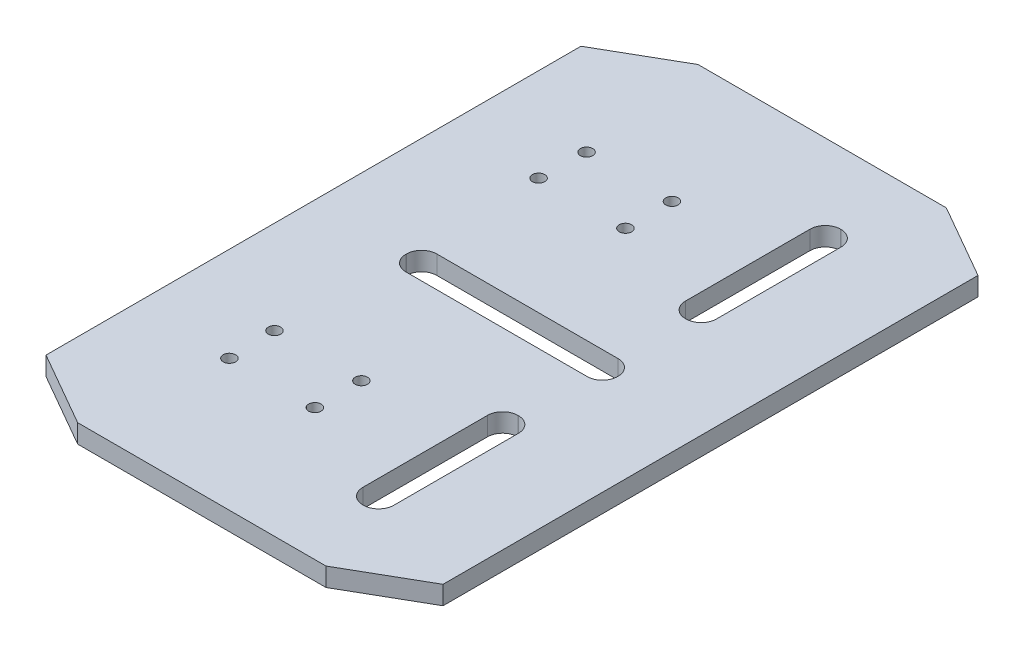
SolidWorks part; units mm, degrees
material "Custom Plastic"
ref_plane "Front Plane" through (0, 0, 0) normal (0, 0, 1) x (1, 0, 0)
ref_plane "Top Plane" through (0, 0, 0) normal (0, 1, 0) x (1, 0, 0)
ref_plane "Right Plane" through (0, 0, 0) normal (1, 0, 0) x (0, 0, -1)
sketch "Sketch1" plane through (0, 0, 0) normal (0, 1, 0) x (1, 0, 0)
  line L0 (-32, -43.1177) -> (-20.0119, -50)
  line L1 (-20.0119, -50) -> (20.0119, -50)
  line L2 (-32, -43.1177) -> (-32, 43.1177)
  line L3 (-20.0119, 50) -> (20.0119, 50)
  line L4 (32, -43.1177) -> (32, 43.1177)
  line L5 (-28.8545, -44.9235) -> (28.8545, 44.9235) construction
  line L6 (-28.4421, 45.1603) -> (28.4421, -45.1603) construction
  line L7 (-114.8204, 0) -> (150.9847, 0) construction
  line L8 (0, -72.5189) -> (0, 84.1411) construction
  line L9 (32, -43.1177) -> (20.0119, -50)
  line L10 (32, 43.1177) -> (20.0119, 50)
  line L11 (-32, 43.1177) -> (-20.0119, 50)
  point P0 (0, 0)
  dimension "D1" = 64
  dimension "D2" = 100
extrude "Boss-Extrude1" add sketch "Sketch1" along normal blind 3
sketch "Sketch5" plane through (0, 3, 0) normal (0, 1, 0) x (1, 0, 0)
  line L0 (-100.8141, 0) -> (111.641, 0) construction
  line L1 (14.5, 50) -> (14.5, -50) construction
  line L2 (-14.6202, -2.5) -> (14.6202, -2.5)
  line L3 (-17.0702, -0.05) -> (-17.0702, 0.05)
  line L4 (-14.6202, 2.5) -> (14.6202, 2.5)
  line L5 (17.0702, -0.05) -> (17.0702, 0.05)
  line L6 (-17.0702, -2.5) -> (17.0702, 2.5) construction
  line L7 (-17.0702, 2.5) -> (17.0702, -2.5) construction
  line L8 (20.0119, 50) -> (-20.0119, 50) construction
  line L9 (-20.0119, -50) -> (20.0119, -50) construction
  line L10 (14.5, 50) -> (14.5, 0) construction
  line L11 (14.5, 0) -> (14.5, -50) construction
  line L12 (14.45, -38.5) -> (14.55, -38.5)
  line L13 (14.45, 13.5) -> (14.55, 13.5)
  line L14 (12, 15.95) -> (12, 36.05)
  line L15 (14.45, 38.5) -> (14.55, 38.5)
  line L16 (17, 15.95) -> (17, 36.05)
  line L17 (12, 13.5) -> (17, 38.5) construction
  line L18 (12, 38.5) -> (17, 13.5) construction
  line L19 (12, -15.95) -> (12, -36.05)
  line L20 (14.45, -13.5) -> (14.55, -13.5)
  line L21 (17, -15.95) -> (17, -36.05)
  line L22 (32, -43.1177) -> (32, 43.1177) construction
  arc A0 (14.45, -38.5) -> (12, -36.05) centre (14.45, -36.05) cw
  arc A1 (14.55, -38.5) -> (17, -36.05) centre (14.55, -36.05) ccw
  arc A2 (12, -15.95) -> (14.45, -13.5) centre (14.45, -15.95) cw
  arc A3 (14.55, -13.5) -> (17, -15.95) centre (14.55, -15.95) cw
  arc A4 (-14.6202, -2.5) -> (-17.0702, -0.05) centre (-14.6202, -0.05) cw
  arc A5 (-17.0702, 0.05) -> (-14.6202, 2.5) centre (-14.6202, 0.05) cw
  arc A6 (14.6202, 2.5) -> (17.0702, 0.05) centre (14.6202, 0.05) cw
  arc A7 (14.6202, -2.5) -> (17.0702, -0.05) centre (14.6202, -0.05) ccw
  arc A8 (14.55, 13.5) -> (17, 15.95) centre (14.55, 15.95) ccw
  arc A9 (14.45, 13.5) -> (12, 15.95) centre (14.45, 15.95) cw
  arc A10 (12, 36.05) -> (14.45, 38.5) centre (14.45, 36.05) cw
  arc A11 (14.55, 38.5) -> (17, 36.05) centre (14.55, 36.05) cw
  point P3 (0, 0)
  point P14 (14.5, 0)
  point P15 (14.5, 26)
  point P17 (14.5, -26)
  point P18 (14.5, 26)
  point P31 (12, -38.5)
  point P34 (17, -38.5)
  point P37 (12, -13.5)
  point P40 (17, -13.5)
  dimension "D7" = 2.45
  dimension "D1" = 5
  dimension "D2" = 26
  dimension "D3" = 26
  dimension "D4" = 5
  dimension "D5" = 25
  dimension "D6" = 15
extrude "Cut-Extrude2" cut sketch "Sketch5" against normal blind 10
sketch "Sketch7" plane through (0, 3, 0) normal (0, 1, 0) x (1, 0, 0)
  line L4 (-24, 17.035) -> (-24, 35.535)
  line L5 (4, 17.035) -> (-24, 17.035)
  line L6 (4, 35.535) -> (-24, 35.535)
  line L7 (4, 17.035) -> (4, 35.535)
  line L9 (-23.2876, 32.535) -> (3.7524, 32.535)
  line L10 (-23.7676, 25.035) -> (4.2324, 25.035)
  line L11 (-10, 43.5449) -> (-10, 10.5144) construction
  line L12 (-17, 43.5449) -> (-17, 10.5144) construction
  line L13 (-16.7676, 32.535) -> (-16.7676, 25.035) construction
  line L14 (-23.7676, 28.785) -> (4.2324, 28.785) construction
  line L16 (-32, 43.1177) -> (-32, -43.1177) construction
  circle A0 centre (-16.7676, 28.785) radius 1
  circle A1 centre (-3, 28.785) radius 1
  circle A2 centre (-17, 21.285) radius 1
  circle A3 centre (-3, 21.285) radius 1
  point P12 (-16.7676, 25.035)
  point P17 (-17, 28.785)
  dimension "D5" = 2
  dimension "D1" = 7.5
  dimension "D2" = 7
  dimension "D3" = 14
  dimension "D4" = 3.75
  dimension "D6" = 28
  dimension "D7" = 8
  dimension "D8" = 14
  dimension "D9" = 14
  dimension "D10" = 7.5
  dimension "D11" = 7.5
  dimension "D12" = 7
ref_plane "Plane1" through (0, 0, 0) normal (0, 0, -1) x (-1, 0, 0)
extrude "Cut-Extrude3" cut sketch "Sketch7" against normal blind 11.5 contours A1 | A3 | A2 | A0
ref_plane "Plane2" through (0, 0, 0) normal (0, 0, -1) x (-1, 0, 0)
mirror "Mirror1" about plane through (0, 0, 0) normal (0, 0, -1) of "Cut-Extrude3"
